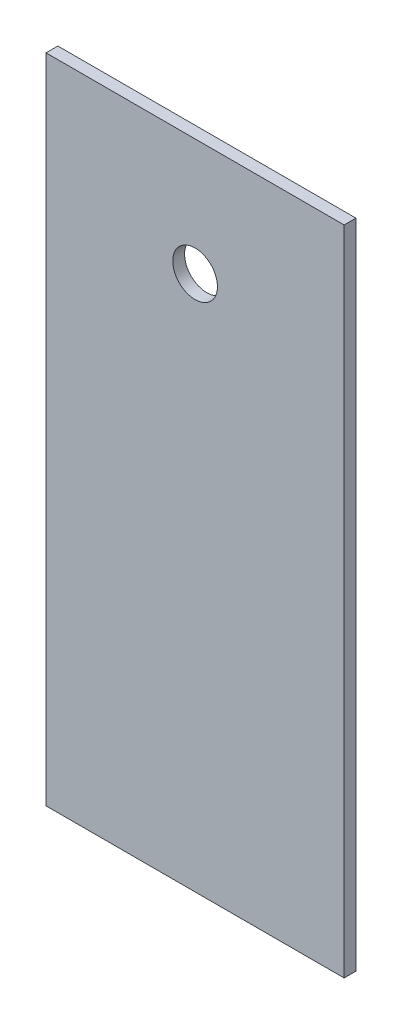
SolidWorks part; units mm, degrees
material "FiberBoard"
ref_plane "Front Plane" through (0, 0, 0) normal (0, 0, 1) x (1, 0, 0)
ref_plane "Top Plane" through (0, 0, 0) normal (0, 1, 0) x (1, 0, 0)
ref_plane "Right Plane" through (0, 0, 0) normal (1, 0, 0) x (0, 0, -1)
sketch "Sketch1" plane through (0, 0, 0) normal (0, 0, 1) x (1, 0, 0)
  line L1 (-40, 87.5) -> (40, 87.5)
  line L2 (-40, 87.5) -> (-40, -87.5)
  line L3 (-40, -87.5) -> (40, -87.5)
  line L4 (40, 87.5) -> (40, -87.5)
  line L5 (-40, 87.5) -> (40, -87.5) construction
  line L6 (-40, -87.5) -> (40, 87.5) construction
  point P0 (0, 0)
  dimension "D1" = 175
  dimension "D2" = 80
extrude "Boss-Extrude1" add sketch "Sketch1" along normal blind 3.175
hole_wizard "Ø12.0mm Dowel Hole1" positions "Sketch2" profile "Sketch3" hole size "Ø12.0" standard "ANSI Metric" end condition up to next
sketch "Sketch2" plane through (0, 0, 3.175) normal (0, 0, 1) x (1, 0, 0)
  line L0 (-40, -87.5) -> (40, -87.5) construction
  point P0 (0, 56.15)
  dimension "D1" = 143.65
sketch "Sketch3" plane through (0, 56.15, 3.175) normal (1, 0, 0) x (0, -1, 0)
  line L0 (0, 0) -> (0, 3.175)
  line L1 (0, 3.175) -> (6, 3.175)
  line L2 (6, 3.175) -> (6, 0)
  line L5 (6, 0) -> (0, 0)
  line L11 (0, -6.35) -> (0, 107.95) construction
  dimension "Thru Hole Dia." = 12
  dimension "Thru Hole Depth" = 3.175
